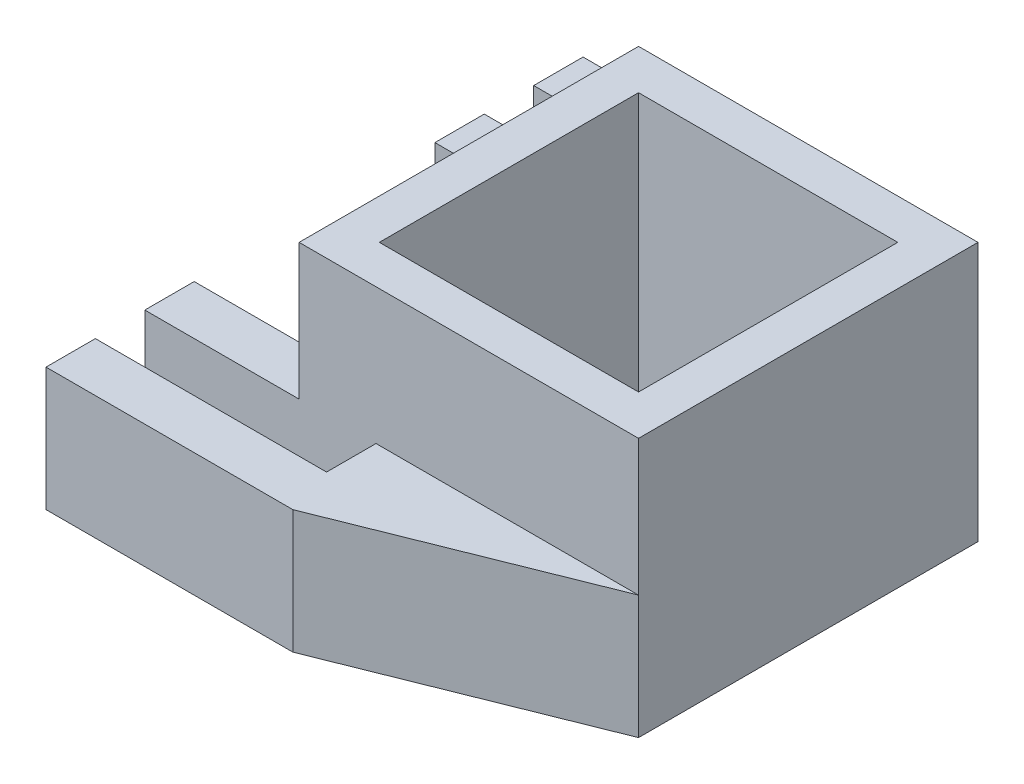
SolidWorks part; units mm, degrees
ref_plane "Front Plane" through (0, 0, 0) normal (0, 0, 1) x (1, 0, 0)
ref_plane "Top Plane" through (0, 0, 0) normal (0, 1, 0) x (1, 0, 0)
ref_plane "Right Plane" through (0, 0, 0) normal (1, 0, 0) x (0, 0, -1)
sketch "Sketch1" plane through (0, 0, 0) normal (0, 1, 0) x (1, 0, 0)
  line L1 (0, 0) -> (42, 0)
  line L2 (0, 0) -> (0, 42)
  line L3 (0, 42) -> (42, 42)
  line L4 (42, 0) -> (42, 42)
  line L5 (-6.5, -6.5) -> (48.5, -6.5)
  line L6 (-6.5, -6.5) -> (-6.5, 48.5)
  line L7 (-6.5, 48.5) -> (48.5, 48.5)
  line L8 (48.5, -6.5) -> (48.5, 48.5)
  dimension "D1" = 55
  dimension "D2" = 55
  dimension "D3" = 42
  dimension "D4" = 42
  dimension "D5" = 6.5
  dimension "D6" = 6.5
extrude "Boss-Extrude1" add sketch "Sketch1" along normal blind 42
sketch "Sketch2" plane through (0, 0, 0) normal (0, -1, 0) x (1, 0, 0)
  line L0 (5.96, 6.5) -> (5.96, 14.51)
  line L1 (-6.5, 6.5) -> (48.5, 6.5) construction
  line L2 (5.96, 14.51) -> (-31.5, 14.51)
  line L3 (-31.5, 14.51) -> (-31.5, 22.51)
  line L6 (-6.5, -21) -> (48.5, -21) construction
  line L7 (8.5, 22.51) -> (48.5, 6.5)
  line L8 (-31.5, 22.51) -> (8.5, 22.51)
  line L9 (-6.5, -48.5) -> (-6.5, 6.5) construction
  line L16 (48.5, 6.5) -> (5.96, 6.5)
  line L17 (48.5, -48.5) -> (5.96, -48.5)
  line L18 (-31.5, -64.51) -> (8.5, -64.51)
  line L19 (8.5, -64.51) -> (48.5, -48.5)
  line L20 (-31.5, -56.51) -> (-31.5, -64.51)
  line L21 (5.96, -56.51) -> (-31.5, -56.51)
  line L22 (5.96, -48.5) -> (5.96, -56.51)
  line L23 (-31.5, -48.5) -> (-31.5, -40.5)
  line L24 (-6.5, 6.5) -> (-31.5, 6.5)
  line L25 (-6.5, 6.5) -> (-6.5, -1.5)
  line L26 (-6.5, -1.5) -> (-31.5, -1.5)
  line L27 (-31.5, 6.5) -> (-31.5, -1.5)
  line L28 (-6.5, -40.5) -> (-31.5, -40.5)
  line L29 (-6.5, -48.5) -> (-31.5, -48.5)
  line L30 (-6.5, -48.5) -> (-6.5, -40.5)
  point P12 (-6.5, -21)
  dimension "D1" = 8.01
  dimension "D2" = 8
  dimension "D3" = 40
  dimension "D4" = 40
  dimension "D5" = 42.54
extrude "Boss-Extrude2" add sketch "Sketch2" against normal blind 20
